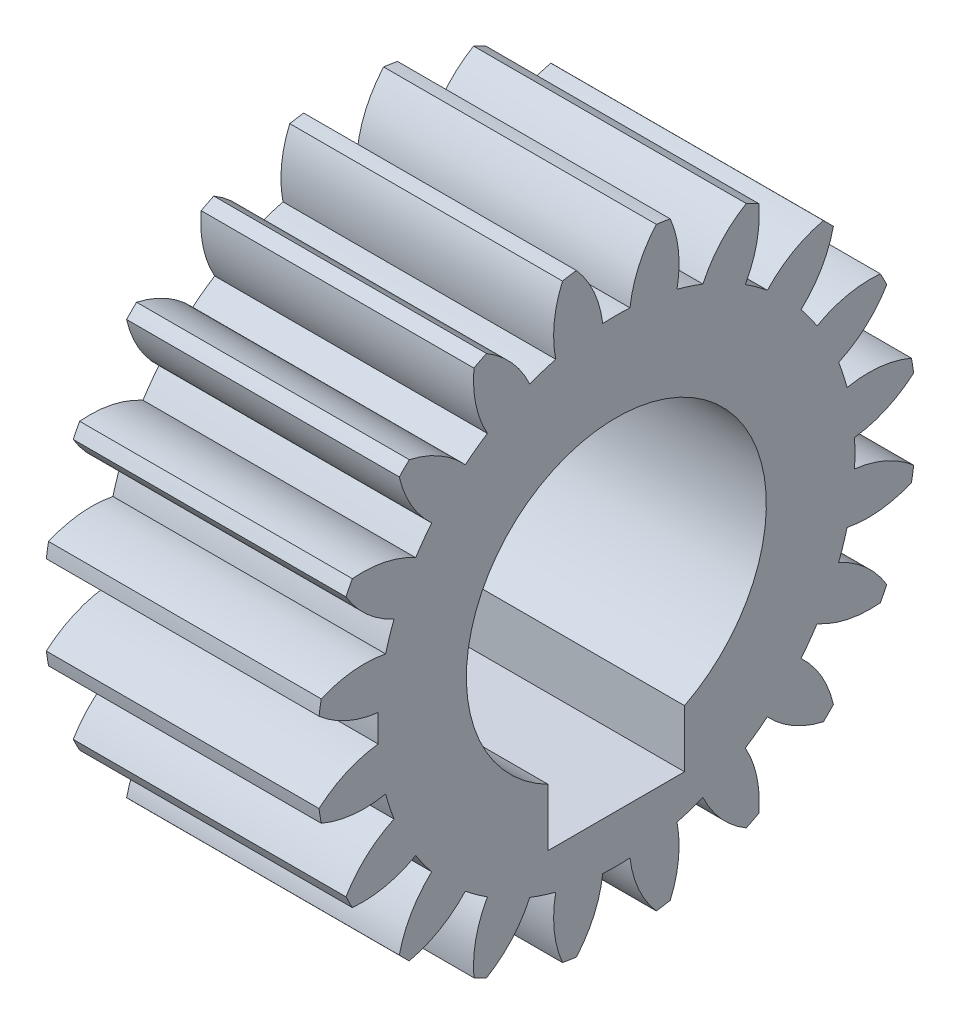
SolidWorks part; units mm, degrees
ref_plane "Plane1" through (0, 0, 0) normal (0, 0, 1) x (1, 0, 0)
ref_plane "Plane2" through (0, 0, 0) normal (0, 1, 0) x (1, 0, 0)
ref_plane "Plane3" through (0, 0, 0) normal (1, 0, 0) x (0, 0, -1)
sketch "HoldingSke" plane through (0, 0, 0) normal (0, 1, 0) x (1, 0, 0)
  line L0 (0, 0) -> (1.8794, -0.684)
  line L1 (-15, 0) -> (100, 0) construction
  line L2 (0, 0) -> (-2.1039, 2.3779)
  line L3 (0, 0) -> (-11.863, 4.5341)
  line L4 (0, 0) -> (8.1152, 2.9537)
  line L5 (0, 0) -> (-46.8476, -17.4728)
  line L6 (0, 0) -> (-4.1448, -2.7965)
  line L7 (-2.1039, 2.3779) -> (8.6586, 51.2059)
  line L8 (-76.2, 54.61) -> (-76.1, 54.61)
  line L9 (-71.009, 38.7566) -> (-53.1078, 45.2721)
  line L10 (-76.2, 71.12) -> (104.1128, 71.12)
  line L11 (0, 0) -> (-5, 0)
  line L12 (-76.2, 101.6) -> (-76.181, 101.6)
  line L13 (24.9733, 27.94) -> (52.9518, 28.4284)
  line L14 (24.9733, 27.94) -> (24.9743, 27.94)
  line L15 (24.9733, 27.94) -> (100.4006, 29.5858)
  line L16 (-63.627, -0.5) -> (-12.827, -0.5)
  circle A0 centre (0, 0) radius 0.5
  circle A1 centre (0, 0) radius 4.374
  circle A2 centre (0, 0) radius 37.5
  circle A3 centre (0, 0) radius 0.5
  dimension "MHD" = 8.748
  dimension "Hub_dia" = 75
  dimension "Bore" = 1
  dimension "MBD" = 1
  dimension "Num_teeth" = 20
  dimension "Pitch" = 2
  dimension "Overall_len" = 50
  dimension "Show_teeth" = 20
  dimension "Thickness" = 5
  dimension "OAL" = 50.0001
  dimension "T_dim" = 0.1
  dimension "Ap" = 20
  dimension "H" = 19.05
  dimension "Pitch_radius" = 180.3128
  dimension "Width" = 5
  dimension "Backlash" = 0.019
  dimension "Addendum_fac" = 1
  dimension "Dedendum_fac" = 1.25
  dimension "Clearance_fac" = 0.25
  dimension "Dedendum_add" = 0.001
  dimension "Module" = 0.5
sketch "BasProSke" plane through (0, 0, 0) normal (0, 1, 0) x (1, 0, 0)
  line L0 (-10, 0) -> (60, 0) construction
  line L1 (0, 0) -> (0, 5.5)
  line L2 (0, 0) -> (5, 0)
  line L3 (5, 0) -> (5, 5.5)
  line L4 (5, 5.5) -> (0, 5.5)
  dimension "Thickness" = 5
  dimension "Diameter" = 11
revolve "Base-Revolve" add sketch "BasProSke" angle 360 about L0
sketch "TooCutSke" plane through (0, 0, 0) normal (1, 0, 0) x (0, 0, -1)
  line L1 (0, 0) -> (0, 107) construction
  line L2 (0, 0) -> (-0.4255, 4.9819) construction
  line L3 (0, 0) -> (-1.5603, 9.8514) construction
  line L4 (-0.4255, 4.9819) -> (-0.7802, 4.9257) construction
  arc A0 (0.2499, 4.3669) -> (-0.2499, 4.3669) centre (0, 0) ccw
  arc A1 (0.7528, 5.4739) -> (-0.7528, 5.4739) centre (0, 0) ccw
  circle A2 centre (0, 0) radius 5 construction
  circle A3 centre (0, 0) radius 4.6985 construction
  arc A4 (-0.2499, 4.3669) -> (-0.7528, 5.4739) centre (-2.2361, 4.1322) ccw
  arc A5 (0.7528, 5.4739) -> (0.2499, 4.3669) centre (2.2361, 4.1322) ccw
  dimension "Root_dia" = 8.748
  dimension "Overcut_dia" = 11.0508
  dimension "Pitch_dia" = 10
  dimension "Base_dia" = 9.3969
  dimension "Flank_rad" = 2
  dimension "Half_ang" = 9
  dimension "Half_CT" = 0.359
extrude "ToothCut" cut sketch "TooCutSke" along normal through all
fillet "Breaks" [suppressed] radius 0.01
fillet "RootFillets" [suppressed] radius 0.126
pattern_circular "TeethCuts" count 20 every 18 about axis through (-10, 0, 0) along (1, 0, 0) of "ToothCut", "RootFillets", "Breaks"
sketch "HubNeaOneSke" plane through (0, 0, 0) normal (-1, 0, 0) x (0, 0, 1)
  circle A0 centre (0, 0) radius 4.374
  dimension "Diameter" = 8.748
extrude "HubNearOne" [suppressed] add sketch "HubNeaOneSke" along normal blind 45.0001
sketch "HubNeaBotSke" plane through (0, 0, 0) normal (-1, 0, 0) x (0, 0, 1)
  circle A0 centre (0, 0) radius 4.374
  dimension "Diameter" = 8.748
extrude "HubNearBoth" [suppressed] add sketch "HubNeaBotSke" along normal blind 22.5
ref_plane "FarPln" through (5, 0, 0) normal (1, 0, 0) x (0, 0, -1)
sketch "HubFarSke" plane through (5, 0, 0) normal (1, 0, 0) x (0, 0, -1)
  circle A0 centre (0, 0) radius 4.374
  dimension "Diameter" = 8.748
extrude "HubFar" [suppressed] add sketch "HubFarSke" along normal blind 22.5
sketch "BorSke" plane through (0, 0, 0) normal (1, 0, 0) x (0, 0, -1)
  circle A0 centre (0, 0) radius 0.5
  dimension "Diameter" = 1
extrude "Bore" cut sketch "BorSke" along normal mid plane 100.0001
sketch "KeySke" plane through (0, 0, 0) normal (1, 0, 0) x (0, 0, -1)
  line L0 (-0.05, 0) -> (-0.05, 0.6)
  line L1 (-0.05, 0.6) -> (0.05, 0.6)
  line L2 (0.05, 0.6) -> (0.05, 0)
  line L3 (0, 0) -> (0, 34) construction
  line L4 (-0.05, 0) -> (0.05, 0)
  dimension "Offset" = 0.6
  dimension "Width" = 0.1
extrude "Keyway" [suppressed] cut sketch "KeySke" along normal mid plane 100.0001
pattern_circular "Keyway2" [suppressed] count 2 every 90 about axis through (-10, 0, 0) along (1, 0, 0)
sketch "Sketch1" plane through (5, 0, 0) normal (1, 0, 0) x (0, 0, -1)
  line L0 (0, 0) -> (0, -8.1441) construction
  line L1 (-1.25, -1.7594) -> (-1.25, -3.5)
  line L2 (-1.25, -1.7594) -> (1.25, -1.7594)
  line L3 (-1.25, -3.5) -> (1.25, -3.5)
  line L4 (1.25, -1.7594) -> (1.25, -3.5)
  line L5 (0, -3.5) -> (0, -1.7594) construction
  line L6 (-1.25, -2.6297) -> (1.25, -2.6297) construction
  circle A0 centre (0, 0) radius 2.75
  point P3 (0, -2.75)
  point P6 (0, -2.6297)
  dimension "D1" = 5.5
  dimension "D2" = 3.5
  dimension "D3" = 2.5
extrude "Cut-Extrude1" cut sketch "Sketch1" against normal through all both and the other way through all contours L4 A0 L1 L2 | A0 L1 L3 L4 | L1 A0 L4 L2
sketch "Sketch2" plane through (0, 0, 0) normal (1, 0, 0) x (0, 0, -1)
  circle A0 centre (0, 0) radius 5
  dimension "D1" = 10
equation "' \"Module@HoldingSke\" = 6.35"
equation "' \"Num_teeth@HoldingSke\" = 12"
equation "' \"Ap@HoldingSke\" =  20"
equation "' \"Ap@HoldingSke\" = 20"
equation "' \"Width@HoldingSke\" = 0.5 * 25.4"
equation "' \"Hub_dia@HoldingSke\"= 1 * 25.4"
equation "' \"Hub_dia@HoldingSke\" = 1 * 25.4"
equation "' \"Overall_len@HoldingSke\" = 1.0 * 25.4"
equation "' \"Bore@HoldingSke\" = 0.75 * 25.4"
equation "' \"T_dim@HoldingSke\" = 0.1 * 25.4"
equation "' \"Width@KeySke\" = 0.25 * 25.4"
equation "' \"Show_teeth@HoldingSke\" = 13"
equation "' \"Backlash@HoldingSke\" = 0.009 * 25.4"
equation "' \"Addendum_fac@HoldingSke\" = 1.0"
equation "' \"Dedendum_fac@HoldingSke\" = 1.25"
equation "' \"Dedendum_add@HoldingSke\" = 0.00005 * 25.4"
equation "' \"Clearance_fac@HoldingSke\" = 0.25"
equation "\"Pitch@HoldingSke\" = 1 / \"Module@HoldingSke\""
equation "\"Overcut_dia@TooCutSke\" = (\"Num_teeth@HoldingSke\" + 2 * \"Addendum_fac@HoldingSke\") / \"Pitch@HoldingSke\" + 0.002 * 25.4"
equation "\"Pitch_dia@TooCutSke\" = \"Num_teeth@HoldingSke\" / \"Pitch@HoldingSke\""
equation "\"Base_dia@TooCutSke\" = \"Num_teeth@HoldingSke\" / \"Pitch@HoldingSke\" * cos((\"Ap@HoldingSke\"  * 3.14159265 / 180))"
equation "\"Root_dia@TooCutSke\" = (\"Num_teeth@HoldingSke\" + 2) / \"Pitch@HoldingSke\" - 2 * (\"Addendum_fac@HoldingSke\" + \"Dedendum_fac@HoldingSke\") / \"Pitch@HoldingSke\" - \"Dedendum_add@HoldingSke\" * 2"
equation "\"Half_ang@TooCutSke\" = 180 / \"Num_teeth@HoldingSke\""
equation "\"Half_CT@TooCutSke\" = \"Num_teeth@HoldingSke\" / \"Pitch@HoldingSke\" * sin((3.14159265 / 2 / \"Num_teeth@HoldingSke\")) / 2 - 7 * \"Backlash@HoldingSke\" / 4"
equation "\"Flank_rad@TooCutSke\" = \"Num_teeth@HoldingSke\" / \"Pitch@HoldingSke\" / 5"
equation "\"Radius@RootFillets\" = \"Clearance_fac@HoldingSke\" / \"Pitch@HoldingSke\" + \"Dedendum_add@HoldingSke\""
equation "\"Break_rad@Breaks\" = 0.02 / \"Pitch@HoldingSke\""
equation "\"Thickness@HoldingSke\" = \"Width@HoldingSke\""
equation "\"OAL@HoldingSke\" = \"Thickness@HoldingSke\""
equation "\"MHD@HoldingSke\" = (\"Num_teeth@HoldingSke\" + 2) / \"Pitch@HoldingSke\" - 2 * (\"Addendum_fac@HoldingSke\" + \"Dedendum_fac@HoldingSke\")  / \"Pitch@HoldingSke\" - \"Dedendum_add@HoldingSke\" * 2"
equation "\"MBD@HoldingSke\" = (\"Num_teeth@HoldingSke\" + 2) / \"Pitch@HoldingSke\" - 2 * (\"Addendum_fac@HoldingSke\" + \"Dedendum_fac@HoldingSke\")  / \"Pitch@HoldingSke\" - \"Dedendum_add@HoldingSke\" * 2 - 0.002 * 25.4"
equation "\"MHD@HoldingSke\" = ((sgn( \"MHD@HoldingSke\" - \"Hub_dia@HoldingSke\" )-1)*( \"MHD@HoldingSke\" - \"Hub_dia@HoldingSke\" ))/-2+ \"Hub_dia@HoldingSke\""
equation "\"MBD@HoldingSke\" = ((sgn( \"MBD@HoldingSke\" - \"Bore@HoldingSke\" )-1)*( \"MBD@HoldingSke\" - \"Bore@HoldingSke\" ))/-2+ \"Bore@HoldingSke\""
equation "\"OAL@HoldingSke\" = ((sgn( \"OAL@HoldingSke\" - \"Overall_len@HoldingSke\" )+1)*( \"OAL@HoldingSke\" - \"Overall_len@HoldingSke\" ))/2 + \"Overall_len@HoldingSke\" + 0.000002 * 25.4"
equation "\"Num_teeth@TeethCuts\" = int( \"Show_teeth@HoldingSke\" ) + 1"
equation "\"Num_teeth@TeethCuts\" = ((sgn( \"Num_teeth@TeethCuts\" - \"Num_teeth@HoldingSke\" )-1)*( \"Num_teeth@TeethCuts\" - \"Num_teeth@HoldingSke\" ))/-2+ \"Num_teeth@HoldingSke\""
equation "\"Num_teeth@TeethCuts\" = ((sgn( \"Num_teeth@TeethCuts\" - 2.0)+1)*( \"Num_teeth@TeethCuts\" - 2.0))/2 +2.0"
equation "\"Angle@TeethCuts\" = 360.0 / \"Num_teeth@HoldingSke\""
equation "\"Diameter@BasProSke\" = (\"Num_teeth@HoldingSke\" + 2 * \"Addendum_fac@HoldingSke\") / \"Pitch@HoldingSke\""
equation "\"Thickness@BasProSke\"  = \"Thickness@HoldingSke\""
equation "' \"Fillet_rad@BasProSke\" =  \"Thickness@HoldingSke\" * 0.05"
equation "' \"Fillet_rad@BasProSke\" = \"Thickness@HoldingSke\" * 0.05"
equation "\"MHD@HoldingSke\" = ((sgn( \"MHD@HoldingSke\" - \"Root_dia@TooCutSke\" )-1)*( \"MHD@HoldingSke\" - \"Root_dia@TooCutSke\" ))/-2+ \"Root_dia@TooCutSke\""
equation "\"Diameter@HubNeaOneSke\" = \"MHD@HoldingSke\""
equation "\"Length@HubNearOne\" = \"OAL@HoldingSke\" - \"Thickness@BasProSke\""
equation "\"Diameter@HubNeaBotSke\" = \"MHD@HoldingSke\""
equation "\"Length@HubNearBoth\" = ( \"OAL@HoldingSke\" - \"Thickness@BasProSke\" ) / 2.0"
equation "\"Thickness@FarPln\" = \"Thickness@BasProSke\""
equation "\"Diameter@HubFarSke\" = \"MHD@HoldingSke\""
equation "\"Length@HubFar\" = ( \"OAL@HoldingSke\" - \"Thickness@BasProSke\" ) / 2.0"
equation "\"Diameter@BorSke\" = \"MBD@HoldingSke\""
equation "\"D1@Bore\" = \"OAL@HoldingSke\" * 2.0"
equation "\"D1@Keyway\" = \"OAL@HoldingSke\" * 2.0"
equation "\"Offset@KeySke\" = \"T_dim@HoldingSke\" + \"MBD@HoldingSke\" / 2.0"
